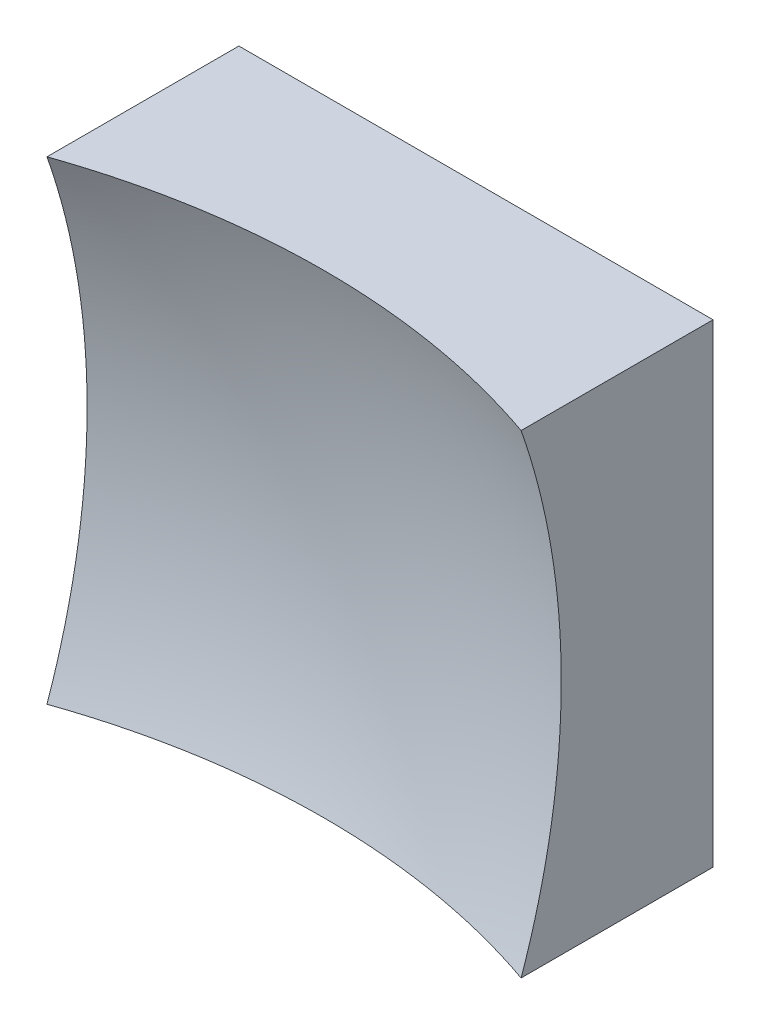
SolidWorks part; units mm, degrees
ref_plane "前视基准面" through (0, 0, 0) normal (0, 0, 1) x (1, 0, 0)
ref_plane "上视基准面" through (0, 0, 0) normal (0, 1, 0) x (1, 0, 0)
ref_plane "右视基准面" through (0, 0, 0) normal (1, 0, 0) x (0, 0, -1)
sketch "草图1" plane through (0, 0, 0) normal (0, 0, 1) x (1, 0, 0)
  line L1 (-6.25, 6.25) -> (6.25, 6.25)
  line L2 (-6.25, 6.25) -> (-6.25, -6.25)
  line L3 (-6.25, -6.25) -> (6.25, -6.25)
  line L4 (6.25, 6.25) -> (6.25, -6.25)
  line L5 (-6.25, 6.25) -> (6.25, -6.25) construction
  line L6 (-6.25, -6.25) -> (6.25, 6.25) construction
  point P0 (0, 0)
  dimension "D1" = 12.5
  dimension "D2" = 12.5
extrude "凸台-拉伸1" add sketch "草图1" along normal blind 10 contours L2 L3 L4 L1
sketch "草图2" plane through (0, 0, 0) normal (0, 1, 0) x (1, 0, 0)
  line L0 (-7.4603, -3) -> (7.3192, -3) construction
  line L1 (0, 0) -> (0, -12.1749) construction
  line L2 (19.4969, -18.5424) -> (0, -18.5424)
  line L3 (0, -18.5424) -> (0, -3)
  arc A1 (19.4969, -18.5424) -> (0, -3) centre (0, -23) ccw
  dimension "D2" = 40
  dimension "D1" = 3
revolve "切除-旋转2" cut sketch "草图2" angle 360 about L3
